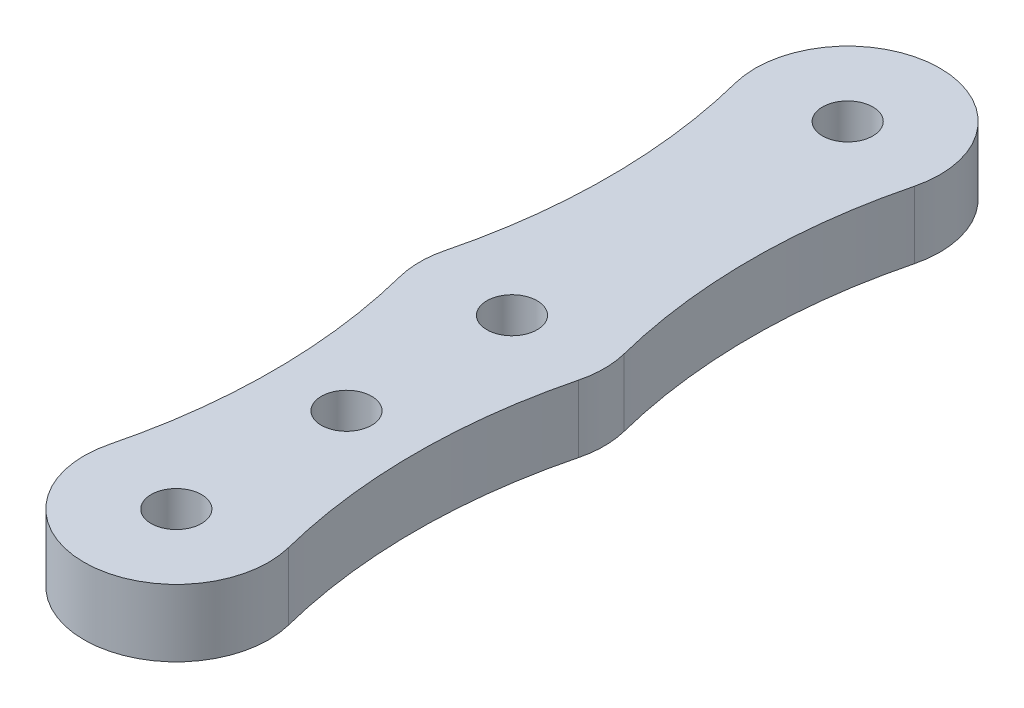
SolidWorks part; units mm, degrees
ref_plane "Front Plane" through (0, 0, 0) normal (0, 0, 1) x (1, 0, 0)
ref_plane "Top Plane" through (0, 0, 0) normal (0, 1, 0) x (1, 0, 0)
ref_plane "Right Plane" through (0, 0, 0) normal (1, 0, 0) x (0, 0, -1)
sketch "Sketch1" plane through (0, 0, 0) normal (0, 1, 0) x (1, 0, 0)
  line L0 (0, 0) -> (0, 40) construction
  line L3 (-4.25, 30) -> (4.25, 30) construction
  line L4 (-4.25, 10) -> (4.25, 10) construction
  circle A2 centre (0, 0) radius 1.5
  circle A3 centre (0, 40) radius 1.5
  arc A8 (-5.3308, 1.3538) -> (5.3308, 1.3538) centre (0, 0) ccw
  arc A9 (5.3308, 38.6462) -> (-5.3308, 38.6462) centre (0, 40) ccw
  circle A12 centre (0, 10.14) radius 1.5
  circle A18 centre (0, 20) radius 1.5
  arc A19 (5.3308, 18.6462) -> (5.3308, 21.3538) centre (0, 20) ccw
  arc A20 (-5.3308, 1.3538) -> (-5.3308, 18.6462) centre (-39.375, 10) ccw
  arc A21 (5.3308, 18.6462) -> (5.3308, 1.3538) centre (39.375, 10) ccw
  arc A22 (-5.3308, 21.3538) -> (-5.3308, 38.6462) centre (-39.375, 30) ccw
  arc A23 (5.3308, 38.6462) -> (5.3308, 21.3538) centre (39.375, 30) ccw
  arc A24 (-5.3308, 21.3538) -> (-5.3308, 18.6462) centre (0, 20) ccw
  point P3 (0, 20)
  point P29 (0, 10)
  dimension "D1" = 3
  dimension "D2" = 40
  dimension "D3" = 4
  dimension "D5" = 3
  dimension "D4" = 8.5
  dimension "D6" = 10.14
  dimension "D7" = 20
extrude "Boss-Extrude1" add sketch "Sketch1" along normal blind 4
